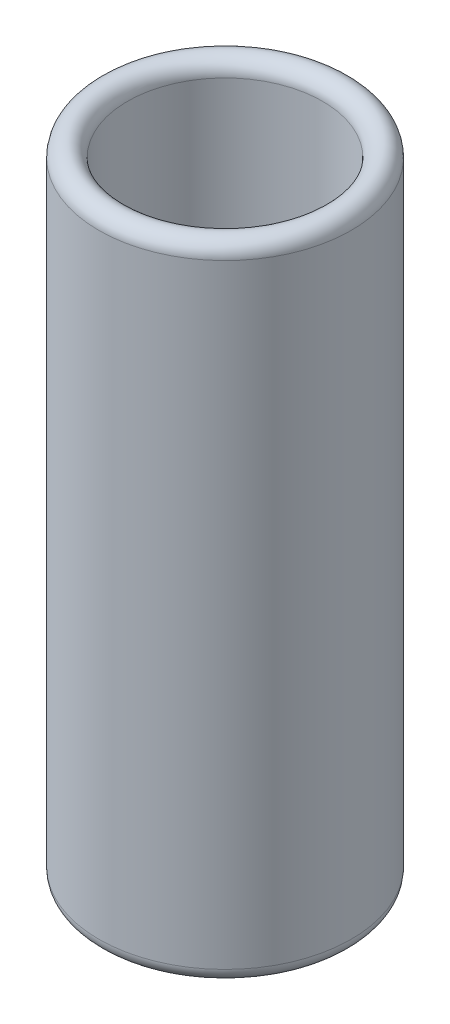
SolidWorks part; units mm, degrees
ref_plane "Plan de face" through (0, 0, 0) normal (0, 0, 1) x (1, 0, 0)
ref_plane "Plan de dessus" through (0, 0, 0) normal (0, 1, 0) x (1, 0, 0)
ref_plane "Plan de droite" through (0, 0, 0) normal (1, 0, 0) x (0, 0, -1)
sketch "Esquisse1" plane through (0, 0, 0) normal (0, 0, 1) x (1, 0, 0)
  line L0 (0, 23.031) -> (0, -1.759) construction
  line L1 (3.4, 21.4) -> (3.4, 0)
  line L2 (4.4, 21.4) -> (4.4, 0)
  arc A0 (4.4, 21.4) -> (3.4, 21.4) centre (3.9, 21.4) ccw
  arc A1 (4.4, 0) -> (3.4, 0) centre (3.9, 0) cw
  dimension "D2" = 0.5
  dimension "D1" = 21.4
  dimension "D3" = 3.4
revolve "Révolution1" add sketch "Esquisse1" angle 360 about L0
